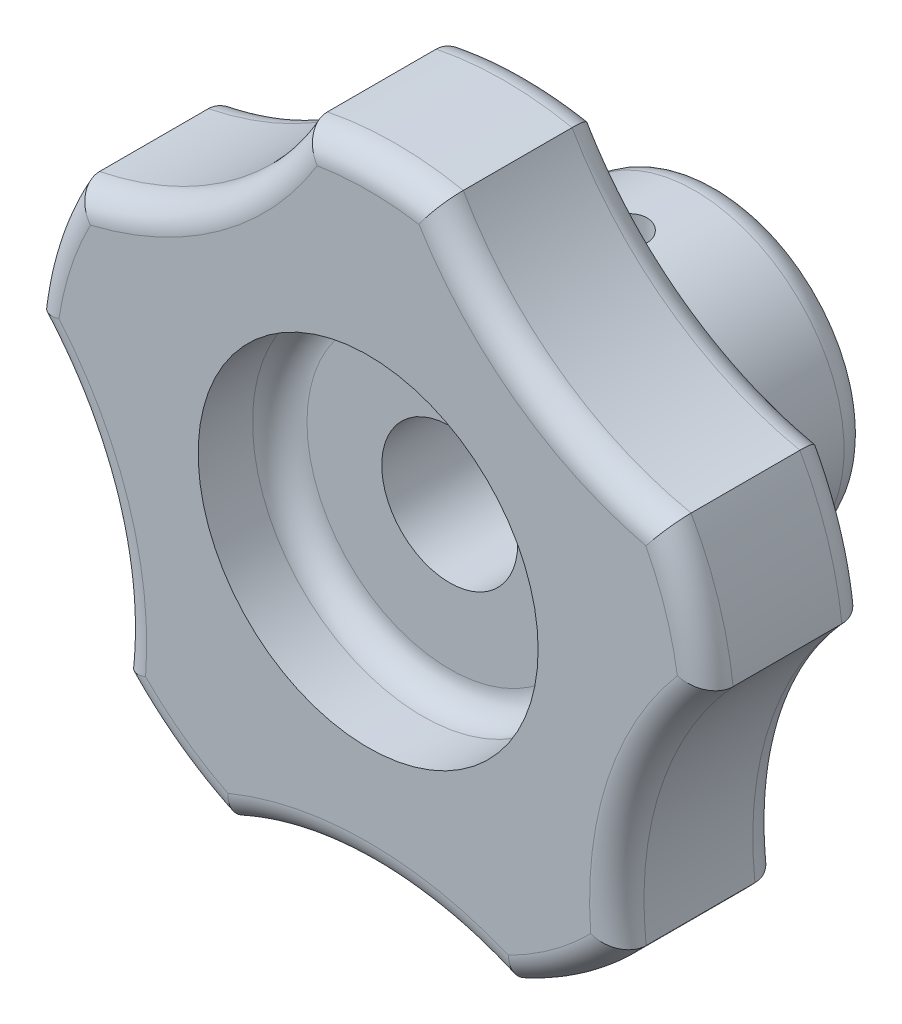
SolidWorks part; units mm, degrees
material "铸造碳钢"
ref_plane "前视基准面" through (0, 0, 0) normal (0, 0, 1) x (1, 0, 0)
ref_plane "上视基准面" through (0, 0, 0) normal (0, 1, 0) x (1, 0, 0)
ref_plane "右视基准面" through (0, 0, 0) normal (1, 0, 0) x (0, 0, -1)
sketch "草图1" plane through (0, 0, 0) normal (0, 1, 0) x (1, 0, 0)
  line L0 (0, 0) -> (0, 26) construction
  line L1 (5, 26) -> (11, 26)
  line L2 (11, 26) -> (11, 12)
  line L3 (11, 12) -> (25, 12)
  line L4 (25, 12) -> (25, 0)
  line L5 (25, 0) -> (12.5, 0)
  line L6 (5, 6) -> (5, 26)
  line L7 (5, 6) -> (12.5, 6)
  line L8 (12.5, 6) -> (12.5, 0)
  dimension "D1" = 26
  dimension "D2" = 5
  dimension "D3" = 11
  dimension "D4" = 12.5
  dimension "D5" = 12
  dimension "D6" = 6
  dimension "D7" = 25
revolve "旋转1" add sketch "草图1" angle 360 about L0
sketch "草图2" plane through (0, 0, 0) normal (0, 0, 1) x (1, 0, 0)
  line L0 (0, 30.414) -> (0, -30.0296) construction
  line L1 (0, 0) -> (30.0793, 41.4005) construction
  line L2 (-5, 30.414) -> (-5, -30.0296) construction
  line L3 (5, 24.4949) -> (5, -30.0296) construction
  line L4 (5, 30.414) -> (5, -30.0296) construction
  circle A0 centre (0, 0) radius 25 construction
  circle A1 centre (0, 0) radius 25
  arc A2 (5, 24.4949) -> (21.7509, 12.3246) centre (26.7509, 36.8195) ccw
  arc A3 (24.8411, 2.8141) -> (18.4428, -16.8779) centre (43.2839, -14.0638) ccw
  arc A4 (10.3527, -22.7557) -> (-10.3527, -22.7557) centre (0, -45.5114) ccw
  arc A5 (-18.4428, -16.8779) -> (-24.8411, 2.8141) centre (-43.2839, -14.0638) ccw
  arc A6 (-21.7509, 12.3246) -> (-5, 24.4949) centre (-26.7509, 36.8195) ccw
  point P29 (0, 0)
  circle M4 centre (0, 0) radius 25
  dimension "D4" = 25
  dimension "D1" = 36
  dimension "D2" = 5
  dimension "D3" = 5
  dimension "D5" = 5
extrude "切除-拉伸1" cut sketch "草图2" against normal up to next contours A6 M4 | A5 M4 | A4 M4 | A3 M4 | A2 M4
sketch "草图3" plane through (0, 0, 0) normal (0, 1, 0) x (1, 0, 0)
  line L0 (11, 26) -> (-11, 26) construction
  circle A0 centre (0, 19) radius 1.5
  dimension "D1" = 3
  dimension "D2" = 7
extrude "切除-拉伸2" cut sketch "草图3" against normal through all both and the other way through all
fillet "圆角1" radius 2 23 edges at (11, 0, -12) (-14.6946, -20.2254, -12) (0, -20.5114, -12) (14.6946, -20.2254, -12) (19.5075, -6.3384, -12) (23.7764, 7.7254, -12) (12.0563, 16.5941, -12) (0, 25, -12) (-12.0563, 16.5941, -12) (-23.7764, 7.7254, -12) (-19.5075, -6.3384, -12) (19.5075, -6.3384, 0) (14.6946, -20.2254, 0) (0, -20.5114, 0) (-14.6946, -20.2254, 0) (-19.5075, -6.3384, 0) (-23.7764, 7.7254, 0) (-12.0563, 16.5941, 0) (0, 25, 0) (12.0563, 16.5941, 0) (23.7764, 7.7254, 0) (11, 0, -26) (12.5, 0, -6)
chamfer "倒角1" distance 1 angle 45 1 edges at (5, 0, -26)
